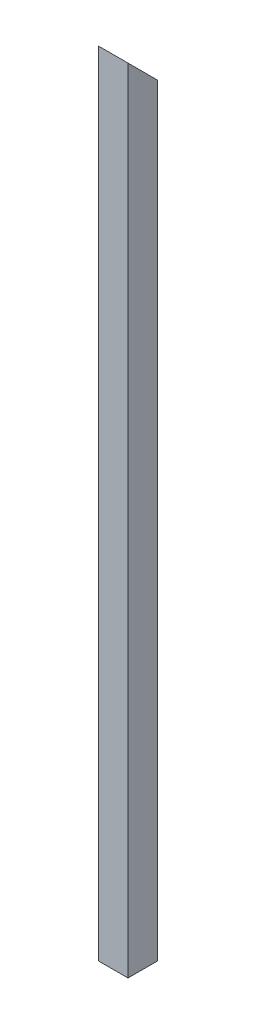
SolidWorks part; units mm, degrees
material "Oak"
ref_plane "Front Plane" through (0, 0, 0) normal (0, 0, 1) x (1, 0, 0)
ref_plane "Top Plane" through (0, 0, 0) normal (0, 1, 0) x (1, 0, 0)
ref_plane "Right Plane" through (0, 0, 0) normal (1, 0, 0) x (0, 0, -1)
sketch "Sketch1" plane through (0, 0, 0) normal (0, 1, 0) x (1, 0, 0)
  line L1 (-9.525, -9.525) -> (9.525, -9.525)
  line L2 (-9.525, -9.525) -> (-9.525, 9.525)
  line L3 (-9.525, 9.525) -> (9.525, 9.525)
  line L4 (9.525, -9.525) -> (9.525, 9.525)
  line L5 (-9.525, -9.525) -> (9.525, 9.525) construction
  line L6 (-9.525, 9.525) -> (9.525, -9.525) construction
  point P0 (0, 0)
  dimension "D1" = 19.05
extrude "Boss-Extrude1" add sketch "Sketch1" along normal blind 533.4
sketch "Sketch4" plane through (9.525, 0, 0) normal (1, 0, 0) x (0, 0, -1)
  line L0 (-9.525, 533.4) -> (-9.525, 0) construction
  line L1 (9.525, 533.4) -> (9.525, 0) construction
  line L3 (9.525, 491.7351) -> (-9.525, 510.7851)
  line L4 (-9.525, 510.7851) -> (-9.525, 533.4)
  line L5 (-9.525, 533.4) -> (9.525, 533.4)
  line L6 (9.525, 533.4) -> (9.525, 491.7351)
  line L7 (-9.525, 533.4) -> (9.525, 533.4) construction
  point P0 (-9.525, 510.7851)
  point P1 (9.525, 491.7351)
  dimension "D1" = 491.7351
  dimension "D2" = 45
extrude "Cut-Extrude1" cut sketch "Sketch4" against normal through all
